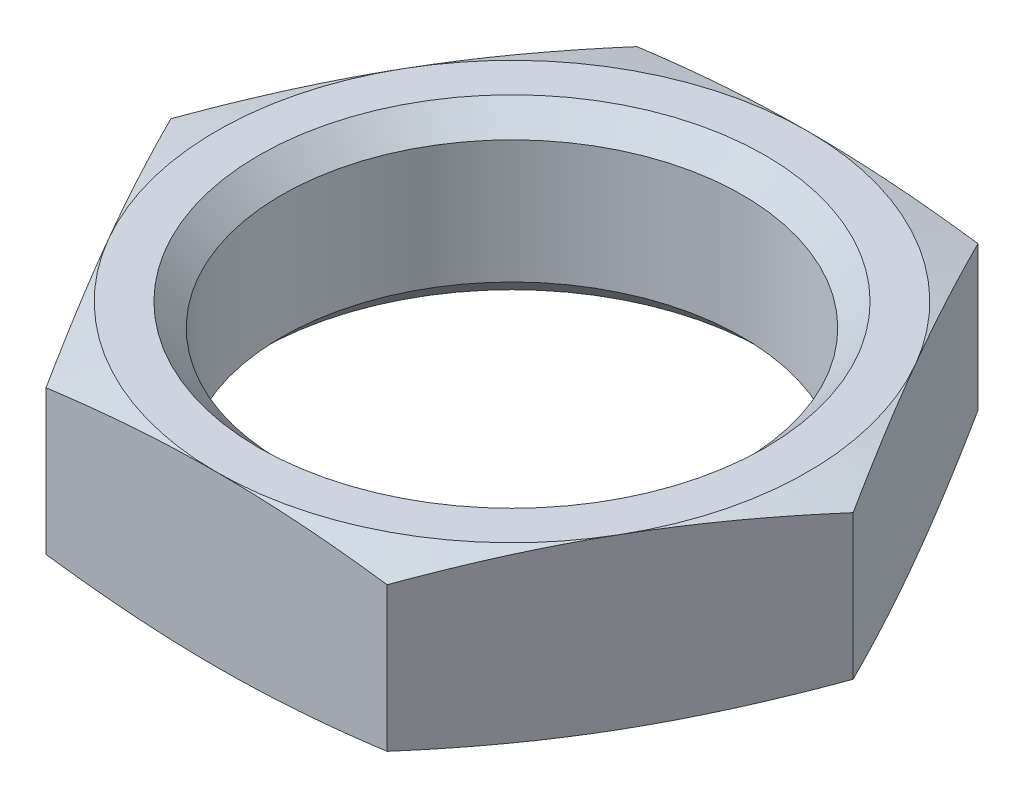
SolidWorks part; units mm, degrees
ref_plane "Front" through (0, 0, 0) normal (0, 0, 1) x (1, 0, 0)
ref_plane "Top" through (0, 0, 0) normal (0, 1, 0) x (1, 0, 0)
ref_plane "Right" through (0, 0, 0) normal (1, 0, 0) x (0, 0, -1)
ref_plane "Plane1" through (0, 0, 0) normal (0, 0, 1) x (1, 0, 0)
sketch "Sketch1" plane through (0, 0, 0) normal (0, 0, 1) x (1, 0, 0)
  line L0 (0, 23) -> (7, 23)
  line L1 (7, 23) -> (8.4, 22.6249)
  line L2 (8.4, 22.6249) -> (8.4, 19.3751)
  line L3 (8.4, 19.3751) -> (7, 19)
  line L4 (7, 19) -> (0, 19)
  line L5 (0, 19) -> (0, 23)
  line L6 (0, 19) -> (0, 23) construction
revolve "Revolve1" add sketch "Sketch1" angle 360 about L6
ref_plane "Plane2" through (0, 0, 0) normal (0, 0, 1) x (1, 0, 0)
sketch "Sketch2" plane through (0, 0, 0) normal (0, 0, 1) x (1, 0, 0)
  line L0 (0, 23) -> (6, 23)
  line L1 (6, 23) -> (5.4585, 22.4585)
  line L2 (5.4585, 22.4585) -> (5.4585, 19.5415)
  line L3 (5.4585, 19.5415) -> (6, 19)
  line L4 (6, 19) -> (0, 19)
  line L5 (0, 19) -> (0, 23)
  line L6 (0, 19) -> (0, 23) construction
revolve "Cut-Revolve1" cut sketch "Sketch2" angle 360 about L6
ref_plane "Plane3" through (0, 19, 0) normal (0, 1, 0) x (-1, 0, 0)
sketch "Sketch3" plane through (0, 19, 0) normal (0, 1, 0) x (-1, 0, 0)
  line L0 (34, 34) -> (-34, 34)
  line L1 (-34, 34) -> (-34, -34)
  line L2 (-34, -34) -> (34, -34)
  line L3 (34, -34) -> (34, 34)
  line L4 (8.0829, 0) -> (4.0415, 7)
  line L5 (4.0415, 7) -> (-4.0415, 7)
  line L6 (-4.0415, 7) -> (-8.0829, 0)
  line L7 (-8.0829, 0) -> (-4.0415, -7)
  line L8 (-4.0415, -7) -> (4.0415, -7)
  line L9 (4.0415, -7) -> (8.0829, 0)
extrude "Cut-Extrude1" cut sketch "Sketch3" along normal blind 4
